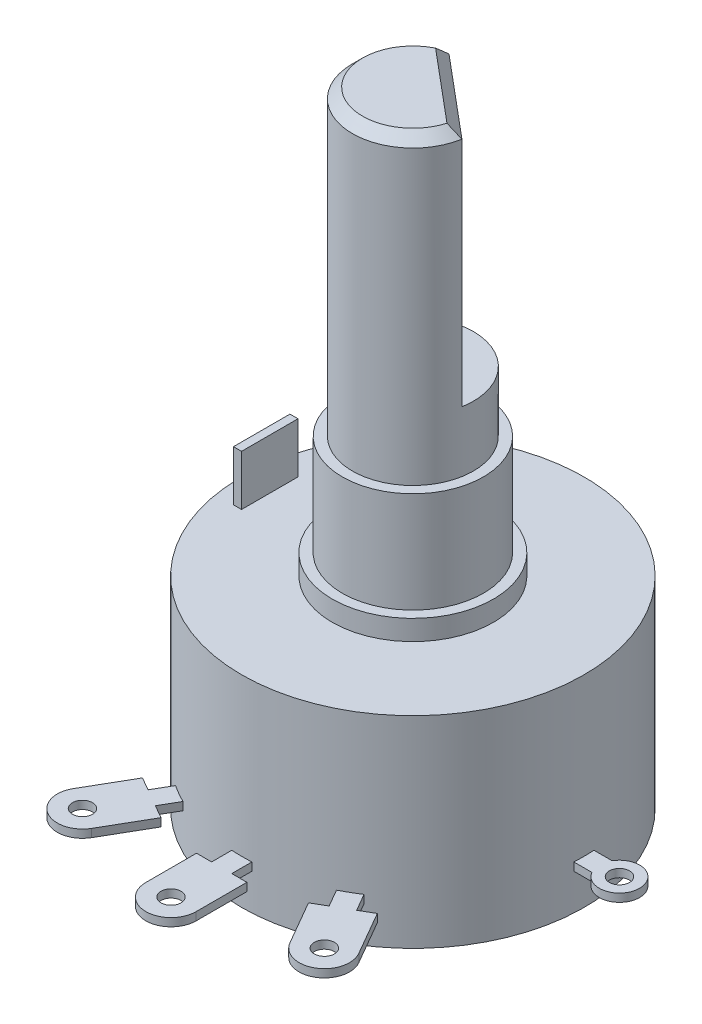
SolidWorks part; units mm, degrees
material "Plain Carbon Steel"
ref_plane "Front Plane" through (0, 0, 0) normal (0, 0, 1) x (1, 0, 0)
ref_plane "Top Plane" through (0, 0, 0) normal (0, 1, 0) x (1, 0, 0)
ref_plane "Right Plane" through (0, 0, 0) normal (1, 0, 0) x (0, 0, -1)
sketch "Sketch1" plane through (0, 0, 0) normal (1, 0, 0) x (0, 0, -1)
  line L0 (0, 0) -> (8.5, 0)
  line L1 (8.5, 0) -> (8.5, 10)
  line L2 (8.5, 10) -> (4, 10)
  line L3 (4, 10) -> (4, 11)
  line L4 (4, 11) -> (3.5, 11)
  line L5 (3.5, 11) -> (3.5, 16)
  line L6 (3.5, 16) -> (0, 16)
  line L7 (0, 16) -> (0, 0) construction
  line L8 (0, 0) -> (0, 16)
  dimension "D1" = 17
  dimension "D2" = 10
  dimension "D3" = 1
  dimension "D4" = 7
  dimension "D5" = 8
  dimension "D6" = 5
revolve "Revolve1" add sketch "Sketch1" angle 360 about L7
sketch "Sketch2" plane through (0, 10, 0) normal (0, 1, 0) x (1, 0, 0)
  line L1 (-7.1, -1.4) -> (-7.5, -1.4)
  line L2 (-7.1, -1.4) -> (-7.1, 1.4)
  line L3 (-7.1, 1.4) -> (-7.5, 1.4)
  line L4 (-7.5, -1.4) -> (-7.5, 1.4)
  line L5 (-7.1, -1.4) -> (-7.5, 1.4) construction
  line L6 (-7.1, 1.4) -> (-7.5, -1.4) construction
  point P0 (-7.3, 0)
  dimension "D1" = 7.5
  dimension "D2" = 0.4
  dimension "D3" = 2.8
extrude "Boss-Extrude1" add sketch "Sketch2" along normal blind 2.5
ref_plane "Plane1" through (0, 2, 0) normal (0, -1, 0) x (-1, 0, 0)
sketch "Sketch3" plane through (0, 2, 0) normal (0, -1, 0) x (-1, 0, 0)
  line L0 (0, -8.5) -> (0, -12) construction
  line L1 (-1.25, -9.4853) -> (-1.25, -12)
  line L2 (1.25, -9.4853) -> (1.25, -12)
  line L3 (1.25, -9.4853) -> (0.5, -9.4853)
  line L4 (0.5, -9.4853) -> (0.5, -8.4853)
  line L5 (-1.25, -9.4853) -> (-0.5, -9.4853)
  line L6 (-0.5, -9.4853) -> (-0.5, -8.4853)
  line L7 (1.25, -8.5) -> (1.25, -12) construction
  line L8 (-1.25, -8.5) -> (-1.25, -12) construction
  line L9 (-5.8252, -7.5895) -> (-7.0825, -9.7673)
  line L10 (-3.6601, -8.8395) -> (-4.9175, -11.0173)
  line L11 (-3.6601, -8.8395) -> (-4.3096, -8.4645)
  line L12 (-4.3096, -8.4645) -> (-3.8096, -7.5985)
  line L13 (-5.8252, -7.5895) -> (-5.1757, -7.9645)
  line L14 (-5.1757, -7.9645) -> (-4.6757, -7.0985)
  line L15 (-4.25, -7.3612) -> (-6, -10.3923) construction
  line L16 (4.25, -7.3612) -> (6, -10.3923) construction
  line L17 (5.1757, -7.9645) -> (4.6757, -7.0985)
  line L18 (5.8252, -7.5895) -> (5.1757, -7.9645)
  line L19 (4.3096, -8.4645) -> (3.8096, -7.5985)
  line L20 (3.6601, -8.8395) -> (4.3096, -8.4645)
  line L21 (3.6601, -8.8395) -> (4.9175, -11.0173)
  line L22 (5.8252, -7.5895) -> (7.0825, -9.7673)
  line L23 (9.75, 0) -> (8.5, 0) construction
  line L24 (9.384, 0.5) -> (8.4853, 0.5)
  line L25 (9.384, -0.5) -> (8.4853, -0.5)
  line L26 (9.25, 0.5) -> (8.5, 0.5) construction
  line L27 (9.25, -0.5) -> (8.5, -0.5) construction
  line L28 (9.25, 0) -> (8.5, 0) construction
  line L29 (-9.75, 0) -> (-8.5, 0) construction
  line L30 (-9.384, -0.5) -> (-8.4853, -0.5)
  line L31 (-9.384, 0.5) -> (-8.4853, 0.5)
  circle A0 centre (0, 0) radius 8.5 construction
  circle A1 centre (0, -12) radius 0.5
  arc A2 (-1.25, -12) -> (1.25, -12) centre (0, -12) ccw
  arc A3 (-0.5, -8.4853) -> (0.5, -8.4853) centre (0, 0) ccw
  circle A4 centre (-6, -10.3923) radius 0.5
  arc A5 (-7.0825, -9.7673) -> (-4.9175, -11.0173) centre (-6, -10.3923) ccw
  arc A6 (-4.6757, -7.0985) -> (-3.8096, -7.5985) centre (0, 0) ccw
  arc A7 (4.6757, -7.0985) -> (3.8096, -7.5985) centre (0, 0) cw
  arc A8 (7.0825, -9.7673) -> (4.9175, -11.0173) centre (6, -10.3923) cw
  circle A9 centre (6, -10.3923) radius 0.5
  circle A10 centre (10.25, 0) radius 0.5
  arc A11 (9.384, -0.5) -> (9.384, 0.5) centre (10.25, 0) ccw
  arc A12 (8.4853, 0.5) -> (8.4853, -0.5) centre (0, 0) cw
  arc A13 (-8.4853, 0.5) -> (-8.4853, -0.5) centre (0, 0) ccw
  arc A14 (-9.384, -0.5) -> (-9.384, 0.5) centre (-10.25, 0) cw
  circle A15 centre (-10.25, 0) radius 0.5
  point P30 (0, 0)
  dimension "D6" = 1
  dimension "D8" = 0.5
  dimension "D10" = 2
  dimension "D11" = 1
  dimension "D1" = 12
  dimension "D2" = 1.25
  dimension "D4" = 0.5
  dimension "D5" = 1
  dimension "D12" = 10.25
  dimension "D3" = 1.25
  dimension "D9" = 0.5
  dimension "D7" = 2
extrude "Boss-Extrude2" add sketch "Sketch3" along normal mid plane 0.4
sketch "Sketch4" plane through (0, 16, 0) normal (0, 1, 0) x (1, 0, 0)
  circle A0 centre (0, 0) radius 3
  dimension "D1" = 6
extrude "Boss-Extrude4" add sketch "Sketch4" along normal blind 15
sketch "Sketch5" plane through (0, 31, 0) normal (0, 1, 0) x (1, 0, 0)
  line L0 (2.9544, -0.5209) -> (-1.0261, 2.8191)
  line L1 (-7.5, 1.4) -> (-7.5, -1.4) construction
  line L2 (0.9642, 1.1491) -> (-1.9284, -2.2981) construction
  circle A0 centre (0, 0) radius 3 construction
  circle A1 centre (0, 0) radius 3
  arc A2 (2.9544, -0.5209) -> (-1.0261, 2.8191) centre (0, 0) ccw
  point P6 (0.9642, 1.1491)
  dimension "D2" = 50
  dimension "D3" = 4.5
  dimension "D1" = 0
extrude "Cut-Extrude1" cut sketch "Sketch5" against normal blind 12
chamfer "Chamfer1" distance 0.5 angle 45 2 edges at (-1.9284, 31, 2.2981) (0.9642, 31, -1.1491)
